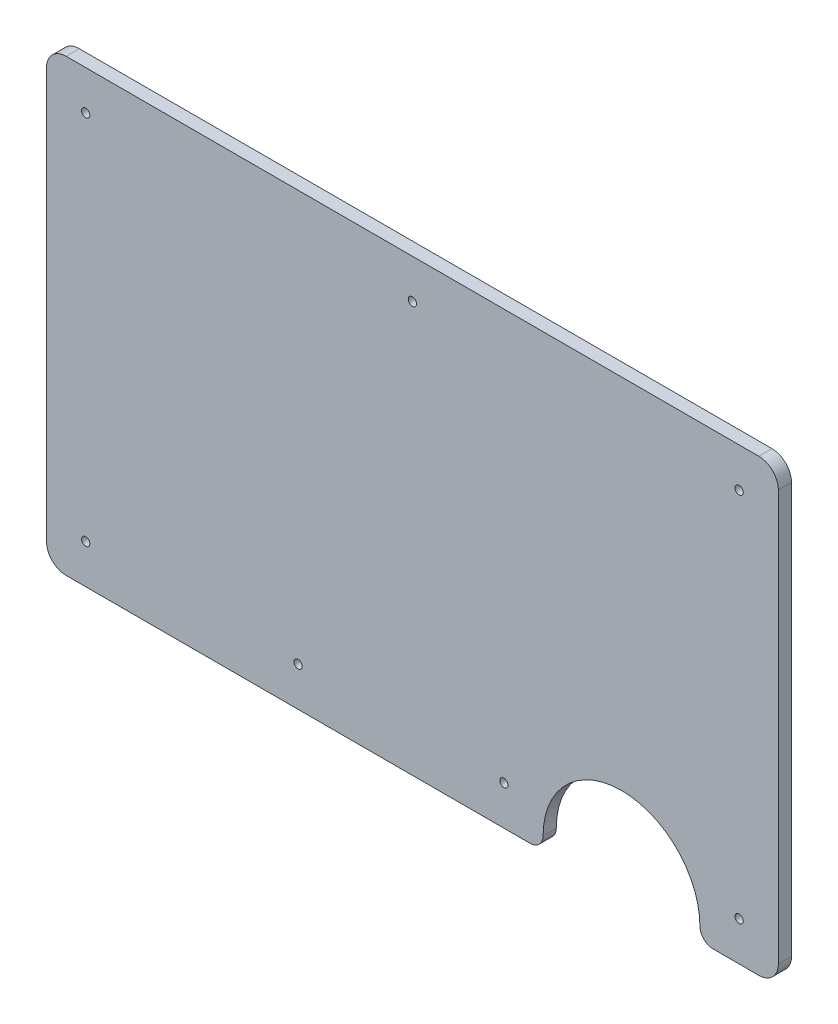
SolidWorks part; units mm, degrees
ref_plane "Front Plane" through (0, 0, 0) normal (0, 0, 1) x (1, 0, 0)
ref_plane "Top Plane" through (0, 0, 0) normal (0, 1, 0) x (1, 0, 0)
ref_plane "Right Plane" through (0, 0, 0) normal (1, 0, 0) x (0, 0, -1)
ref_plane "Plane1" through (0, 0, 1.6) normal (0, 0, 1) x (1, 0, 0)
sketch "Sketch1" plane through (0, 0, 1.6) normal (0, 0, 1) x (1, 0, 0)
  line L0 (0, 53.3207) -> (0, 3.4732)
  line L1 (2.3813, 1.092) -> (58.7375, 1.092)
  line L2 (80.9625, 1.092) -> (86.5187, 1.092)
  line L3 (88.9, 3.4732) -> (88.9, 53.3207)
  line L4 (86.5187, 55.702) -> (2.3813, 55.702)
  line L5 (79.375, -1.3322) -> (79.375, -50001.3322) construction
  line L6 (2.3813, 1.092) -> (58.7375, 1.092) construction
  line L7 (30.5594, 1.092) -> (30.5594, 11.6574) construction
  line L8 (44.45, 55.702) -> (44.45, 38.5848) construction
  circle A0 centre (4.7625, 50.9395) radius 0.5
  circle A1 centre (4.7625, 5.8545) radius 0.5
  circle A2 centre (84.1375, 5.8545) radius 0.5
  circle A3 centre (84.1375, 50.9395) radius 0.5
  circle A4 centre (30.5594, 5.8545) radius 0.5
  circle A5 centre (55.5625, 5.8545) radius 0.5
  circle A6 centre (44.45, 50.9395) radius 0.5
  arc A7 (0, 3.4732) -> (2.3813, 1.092) centre (2.3813, 3.4732) ccw
  arc A8 (58.7375, 1.092) -> (60.325, 2.6795) centre (58.7375, 2.6795) ccw
  arc A9 (60.325, 2.6795) -> (79.375, 2.6795) centre (69.85, 2.6795) cw
  arc A10 (79.375, 2.6795) -> (80.9625, 1.092) centre (80.9625, 2.6795) ccw
  arc A11 (86.5187, 1.092) -> (88.9, 3.4732) centre (86.5187, 3.4732) ccw
  arc A12 (88.9, 53.3207) -> (86.5187, 55.702) centre (86.5187, 53.3207) ccw
  arc A13 (2.3813, 55.702) -> (0, 53.3207) centre (2.3813, 53.3207) ccw
  point P33 (30.5594, 1.092)
  point P37 (44.45, 55.702)
  dimension "D3" = 9.525
  dimension "D4" = 1
  dimension "D5" = 1.5875
  dimension "D14" = 2.3813
  dimension "D1" = 88.9
  dimension "D2" = 54.61
  dimension "D6" = 4.7625
  dimension "D7" = 4.7625
  dimension "D8" = 19.05
  dimension "D9" = 4.7625
  dimension "D10" = 4.7625
  dimension "D11" = 4.7625
  dimension "D12" = 4.7625
  dimension "D13" = 3.175
  dimension "D15" = 4.7625
  dimension "D16" = 4.7625
  dimension "D17" = 4.7625
  dimension "D18" = 4.7625
  dimension "D19" = 4.7625
extrude "Boss-Extrude1" add sketch "Sketch1" against normal blind 1.6
